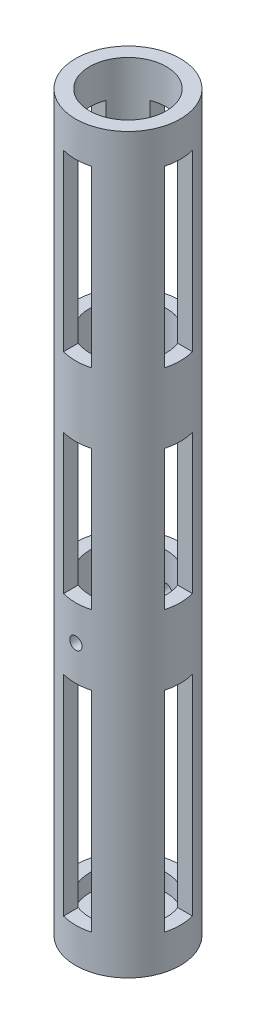
SolidWorks part; units mm, degrees
ref_plane "Front Plane" through (0, 0, 0) normal (0, 0, 1) x (1, 0, 0)
ref_plane "Top Plane" through (0, 0, 0) normal (0, 1, 0) x (1, 0, 0)
ref_plane "Right Plane" through (0, 0, 0) normal (1, 0, 0) x (0, 0, -1)
sketch "Sketch1" plane through (0, 0, 0) normal (0, 1, 0) x (1, 0, 0)
  circle A0 centre (0, 0) radius 13.97
  circle A1 centre (0, 0) radius 19.05
  dimension "D1" = 27.94
  dimension "D2" = 38.1
extrude "Boss-Extrude1" add sketch "Sketch1" along normal blind 266.7
sketch "Sketch2" plane through (0, 0, 0) normal (0, -1, 0) x (1, 0, 0)
  circle A0 centre (0, 0) radius 13.97
extrude "Boss-Extrude2" add sketch "Sketch2" against normal blind 6.35
ref_plane "Plane1" through (0, 0, 16.51) normal (0, 0, 1) x (1, 0, 0)
sketch "Sketch3" plane through (0, 0, 16.51) normal (0, 0, 1) x (1, 0, 0)
  line L0 (-19.05, 0) -> (19.05, 0) construction
  line L1 (0, 101.6) -> (0, 0) construction
  circle A0 centre (0, 101.6) radius 2.2479
  dimension "D1" = 4.4958
  dimension "D2" = 101.6
extrude "Cut-Extrude1" cut sketch "Sketch3" against normal through all and the other way through all contours A0
sketch "Sketch5" plane through (0, 0, 0) normal (1, 0, 0) x (0, 0, -1)
  line L0 (55, 0) -> (-55, 0) construction
  line L1 (5.08, 12.7) -> (-5.08, 12.7)
  line L2 (5.08, 12.7) -> (5.08, 254)
  line L3 (5.08, 254) -> (-5.08, 254)
  line L4 (-5.08, 12.7) -> (-5.08, 254)
  line L5 (19.05, 266.7) -> (-19.05, 266.7) construction
  line L6 (0, 0) -> (0, 12.7) construction
  line L7 (-5.08, 114.3) -> (7.62, 114.3)
  line L8 (-5.08, 88.9) -> (7.62, 88.9)
  line L9 (-5.08, 165.1) -> (5.08, 165.1)
  line L10 (-5.08, 190.5) -> (5.08, 190.5)
  dimension "D1" = 12.7
  dimension "D2" = 12.7
  dimension "D3" = 10.16
  dimension "D4" = 12.7
  dimension "D5" = 12.7
  dimension "D6" = 76.2
  dimension "D7" = 25.4
  dimension "D8" = 25.4
  dimension "D9" = 50.8
extrude "Cut-Extrude5" cut sketch "Sketch5" against normal through all both and the other way through all contours L8 L4 L1 L2 | L9 L4 L7 L2 | L4 L10 L2 L3
sketch "Sketch8" plane through (0, 0, 0) normal (0, 0, 1) x (1, 0, 0)
  line L0 (-19.05, 0) -> (19.05, 0) construction
  line L1 (5.08, 12.7) -> (-5.08, 12.7)
  line L2 (5.08, 12.7) -> (5.08, 254)
  line L3 (5.08, 254) -> (-5.08, 254)
  line L4 (-5.08, 12.7) -> (-5.08, 254)
  line L5 (19.05, 266.7) -> (-19.05, 266.7) construction
  line L6 (0, 12.7) -> (0, 0) construction
  line L7 (5.08, 88.9) -> (-5.08, 88.9)
  line L8 (5.08, 114.3) -> (-5.08, 114.3)
  line L9 (5.08, 165.1) -> (-5.08, 165.1)
  line L10 (5.08, 190.5) -> (-5.08, 190.5)
  dimension "D1" = 12.7
  dimension "D2" = 10.16
  dimension "D3" = 12.7
  dimension "D4" = 76.2
  dimension "D5" = 25.4
  dimension "D6" = 25.4
  dimension "D7" = 50.8
extrude "Cut-Extrude6" cut sketch "Sketch8" against normal through all both and the other way through all contours L2 L7 L4 L1 | L2 L9 L4 L8 | L10 L2 L3 L4
sketch "Sketch7" plane through (0, 6.35, 0) normal (0, 1, 0) x (1, 0, 0)
  circle A0 centre (0, 0) radius 6.35
extrude "Cut-Extrude4" cut sketch "Sketch7" against normal through all
